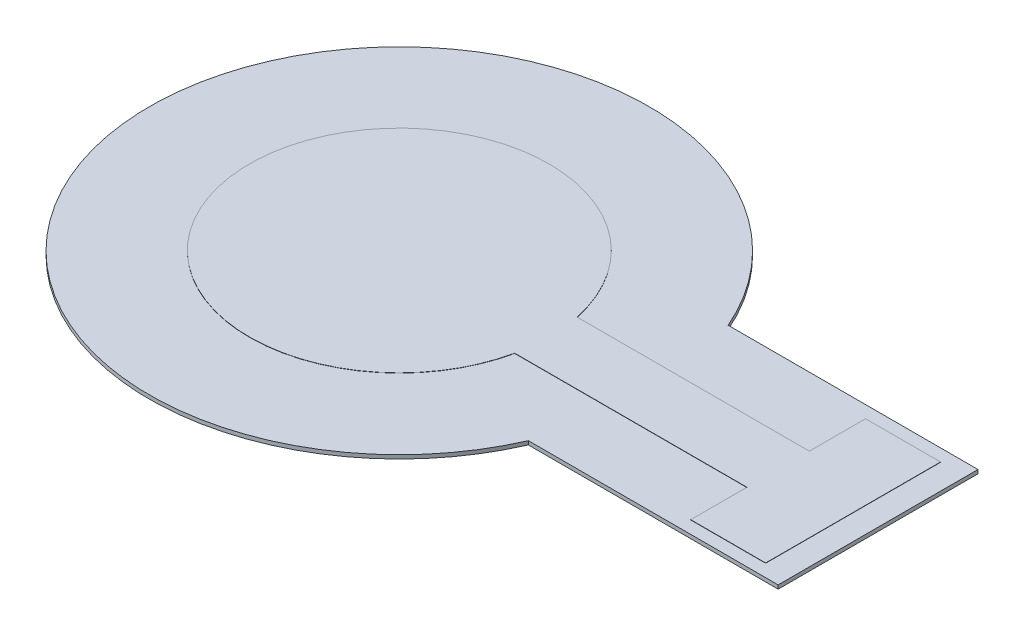
SolidWorks part; units mm, degrees
ref_plane "Front Plane" through (0, 0, 0) normal (0, 0, 1) x (1, 0, 0)
ref_plane "Top Plane" through (0, 0, 0) normal (0, 1, 0) x (1, 0, 0)
ref_plane "Right Plane" through (0, 0, 0) normal (1, 0, 0) x (0, 0, -1)
sketch "Sketch1" plane through (0, 0, 0) normal (0, 1, 0) x (1, 0, 0)
  line L0 (37.7264, 251.4563) -> (27.7264, 251.4563)
  line L1 (27.7264, 243.4563) -> (37.7264, 243.4563)
  line L2 (37.7264, 243.4563) -> (37.7264, 251.4563)
  line L3 (32.8628, 249.9526) -> (23.895, 249.954)
  line L4 (23.9441, 247.1944) -> (32.8628, 247.193)
  line L5 (32.8628, 247.193) -> (32.8628, 244.6365)
  line L6 (32.8628, 244.6365) -> (36.3978, 244.6365)
  line L7 (36.3978, 244.6365) -> (36.3978, 252.1782)
  line L8 (36.3978, 252.1782) -> (32.8628, 252.1782)
  line L9 (32.8628, 252.1782) -> (32.8628, 249.9526)
  arc A0 (27.7264, 251.4563) -> (27.7264, 243.4563) centre (18.5613, 247.4563) ccw
  spline S4 degree 3 poles (19.0975, 253.4948) (17.7715, 253.4804) (16.5056, 252.9398) (15.5781, 251.992) knots 0 0 0 0 1 1 1 1
  spline S5 degree 3 poles (15.5781, 251.992) (14.6408, 251.054) (14.1145, 249.782) (14.115, 248.4559) knots 0 0 0 0 1 1 1 1
  spline S6 degree 3 poles (14.115, 248.4559) (14.1161, 247.1298) (14.644, 245.8585) (15.5826, 244.9217) knots 0 0 0 0 1 1 1 1
  spline S7 degree 3 poles (15.5826, 244.9217) (16.5302, 243.994) (17.8075, 243.4808) (19.1335, 243.4949) knots 0 0 0 0 1 1 1 1
  spline S8 degree 3 poles (19.1335, 243.4949) (21.3876, 243.5027) (23.3578, 245.0178) (23.9441, 247.1944) knots 0 0 0 0 1 1 1 1
  spline S9 degree 3 poles (23.895, 249.954) (23.2515, 252.063) (21.3025, 253.5015) (19.0975, 253.4948) knots 0 0 0 0 1 1 1 1
  dimension "D5" = 20
  dimension "D1" = 10
  dimension "D2" = 10
  dimension "D3" = 8
  dimension "D4" = 4
extrude "Boss-Extrude1" add sketch "Sketch1" along normal blind 0.15
sketch "Sketch2" plane through (0, 0.15, 0) normal (0, 1, 0) x (1, 0, 0)
  line L3 (33.7264, 248.7063) -> (24.4296, 248.7063)
  line L4 (24.4296, 246.2063) -> (33.7264, 246.2063)
  line L5 (33.7264, 246.2063) -> (33.7264, 243.9563)
  line L6 (33.7264, 243.9563) -> (36.7264, 243.9563)
  line L7 (36.7264, 243.9563) -> (36.7264, 250.9563)
  line L8 (36.7264, 250.9563) -> (33.7264, 250.9563)
  line L9 (33.7264, 250.9563) -> (33.7264, 248.7063)
  line L10 (37.7264, 251.4563) -> (27.7264, 251.4563) construction
  line L12 (37.7264, 243.4563) -> (37.7264, 251.4563) construction
  arc A0 (24.4296, 248.7063) -> (24.4296, 246.2063) centre (18.5613, 247.4563) ccw
  arc A1 (27.7264, 251.4563) -> (27.7264, 243.4563) centre (18.5613, 247.4563) ccw construction
  point P1 (18.6288, 247.6934)
  dimension "D1" = 0.5
  dimension "D2" = 7
  dimension "D3" = 2.5
  dimension "D4" = 1.25
  dimension "D5" = 1
  dimension "D6" = 3
extrude "Boss-Extrude2" add sketch "Sketch2" along normal blind 0.01 and the other way blind 0.049 separate body
ref_plane "Plane2" through (0, 0, -248.5063) normal (0, 0, 1) x (1, 0, 0)
